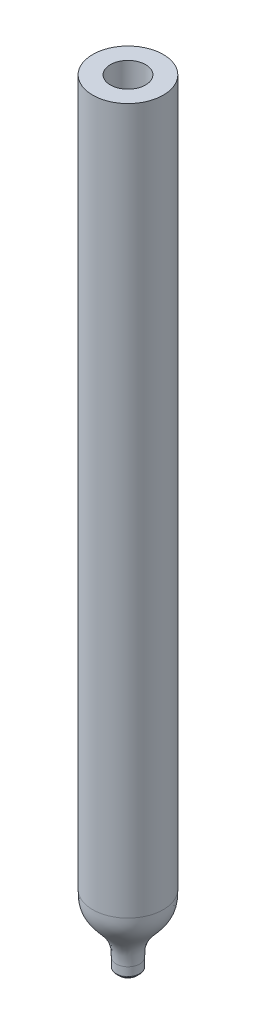
SolidWorks part; units mm, degrees
material "Glass"
ref_plane "Front Plane" through (0, 0, 0) normal (0, 0, 1) x (1, 0, 0)
ref_plane "Top Plane" through (0, 0, 0) normal (0, 1, 0) x (1, 0, 0)
ref_plane "Right Plane" through (0, 0, 0) normal (1, 0, 0) x (0, 0, -1)
sketch "Sketch1" plane through (0, 0, 0) normal (0, 0, 1) x (1, 0, 0)
  line L0 (1.5, 0) -> (0, 0) construction
  line L1 (1.5, 61) -> (3, 61)
  line L2 (1.5, 61) -> (1.5, 0)
  line L3 (0.25, -4) -> (1, -4) construction
  line L4 (3, 61) -> (3, 1)
  line L5 (0, 0) -> (0, -17.1222) construction
  line L6 (3, 1) -> (1.5, 1) construction
  line L8 (0.25, -4) -> (0.25, -5)
  line L9 (0.25, -5) -> (1, -5)
  line L10 (1, -4) -> (1, -5)
  spline S0 degree 3 poles (0.25, -4) (0.25, -3.8743) (0.348, -1.569) (1.4072, -1.5615) (1.5, -0.082) (1.5, 0) knots 0 0 0 0 0.05 0.95 1 1 1 1
  spline S1 degree 5 poles (1, -4) (1, -2.8523) (1, -1.7047) (3, -1.2953) (3, -0.1477) (3, 1) knots 0 0 0 0 0 0 1 1 1 1 1 1
  dimension "D1" = 6
  dimension "D2" = 3
  dimension "D3" = 60
  dimension "D4" = 5
  dimension "D5" = 4
  dimension "D6" = 0.5
  dimension "D7" = 2
  dimension "D8" = 1
revolve "Revolve1" add sketch "Sketch1" angle 360 about L5
chamfer "Chamfer1" distance 0.25 angle 45 1 edges at (0, -5, 1)
fillet "Fillet1" radius 0.1 1 edges at (0, -4.75, 1)
